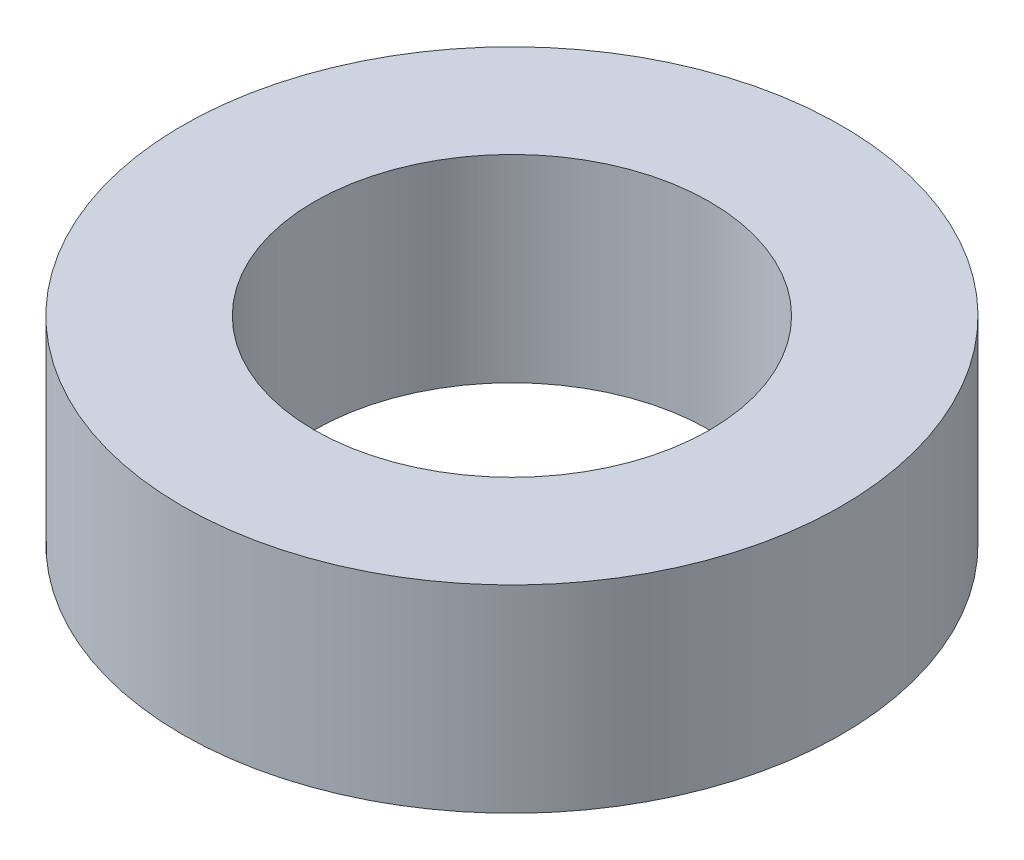
SolidWorks part; units mm, degrees
ref_plane "Front Plane" through (0, 0, 0) normal (0, 0, 1) x (1, 0, 0)
ref_plane "Top Plane" through (0, 0, 0) normal (0, 1, 0) x (1, 0, 0)
ref_plane "Right Plane" through (0, 0, 0) normal (1, 0, 0) x (0, 0, -1)
sketch "Sketch1" plane through (0, 0, 0) normal (0, 1, 0) x (1, 0, 0)
  circle A0 centre (0, 0) radius 3
  circle A1 centre (0, 0) radius 5
  dimension "D1" = 10
  dimension "D2" = 6
extrude "Boss-Extrude1" add sketch "Sketch1" along normal blind 3
